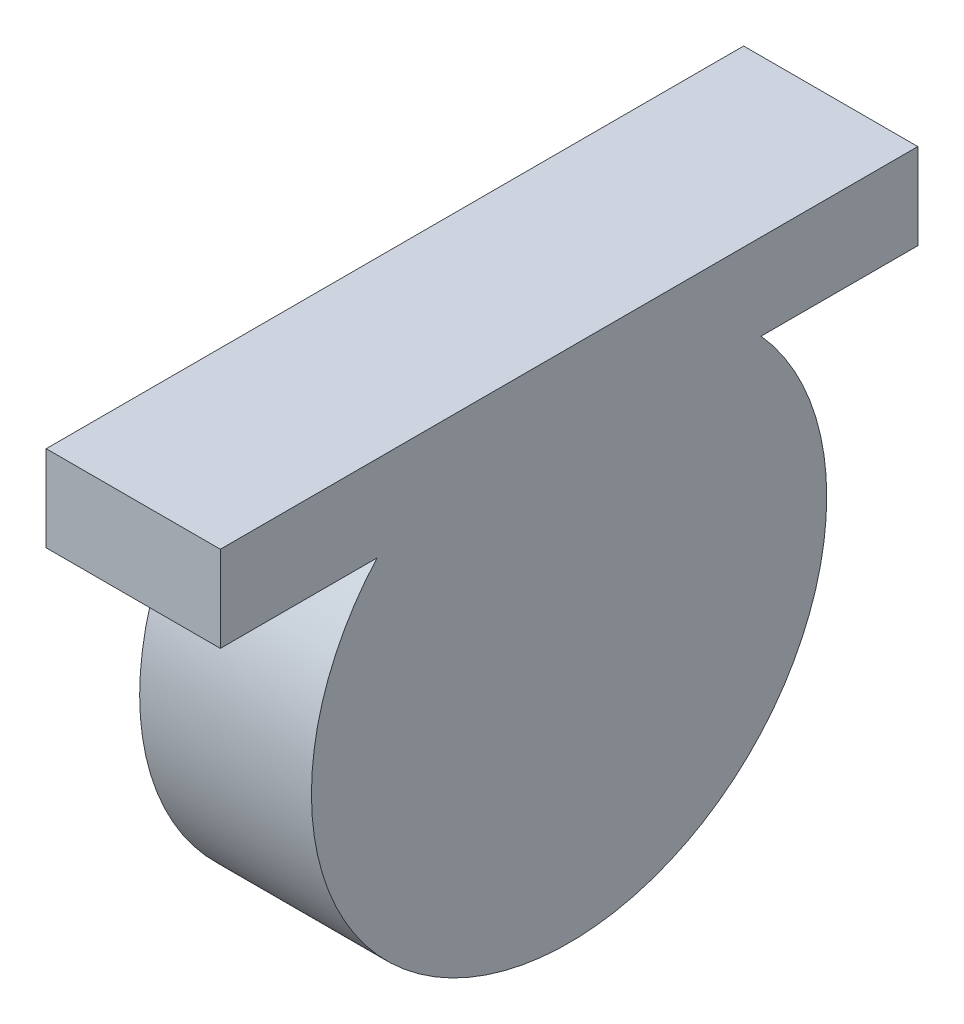
SolidWorks part; units mm, degrees
ref_plane "Front Plane" through (0, 0, 0) normal (0, 0, 1) x (1, 0, 0)
ref_plane "Top Plane" through (0, 0, 0) normal (0, 1, 0) x (1, 0, 0)
ref_plane "Right Plane" through (0, 0, 0) normal (1, 0, 0) x (0, 0, -1)
sketch "Sketch3" plane through (0, 717.6366, 0) normal (0, -1, 0) x (-1, 0, 0)
  line L0 (-524.1514, -762.9166) -> (-524.1514, -558.1792) construction
  line L1 (-524.1514, -712.1166) -> (-498.3984, -712.1166)
  line L2 (-524.1514, -712.1166) -> (-524.1514, -608.9792)
  line L3 (-524.1514, -608.9792) -> (-498.3984, -608.9792)
  line L4 (-498.3984, -712.1166) -> (-498.3984, -608.9792)
  line L5 (-498.3984, -762.9166) -> (-498.3984, -558.1792) construction
  line L6 (-524.1514, -762.9166) -> (-498.3984, -762.9166) construction
  line L7 (-524.1514, -558.1792) -> (-498.3984, -558.1792) construction
  dimension "D1" = 50.8
  dimension "D2" = 50.8
extrude "Boss-Extrude1" add sketch "Sketch3" along normal blind 12.7
sketch "Sketch4" plane through (524.1514, 0, 0) normal (1, 0, 0) x (0, 0, -1)
  line L0 (-660.5479, 717.6366) -> (-660.5479, 679.5366) construction
  line L1 (-608.9792, 717.6366) -> (-712.1166, 717.6366) construction
  circle A0 centre (-660.5479, 679.5366) radius 38.1
  dimension "D1" = 38.1
extrude "Boss-Extrude2" add sketch "Sketch4" against normal blind 25.4
ref_plane "Plane1" through (0, 0, 660.5479) normal (0, 0, 1) x (1, 0, 0)
sketch "Sketch5" plane through (0, 0, 660.5479) normal (0, 0, 1) x (1, 0, 0)
  line L0 (472.4505, 692.7093) -> (547.7665, 668.1914)
